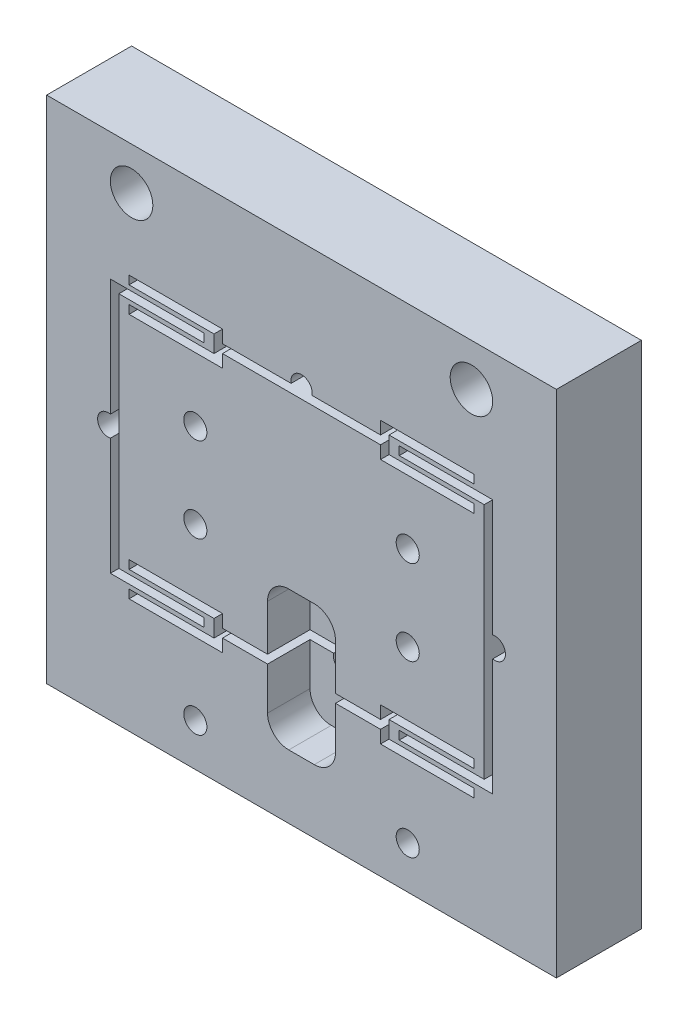
SolidWorks part; units mm, degrees
ref_plane "Front Plane" through (0, 0, 0) normal (0, 0, 1) x (1, 0, 0)
ref_plane "Top Plane" through (0, 0, 0) normal (0, 1, 0) x (1, 0, 0)
ref_plane "Right Plane" through (0, 0, 0) normal (1, 0, 0) x (0, 0, -1)
sketch "Sketch1" plane through (0, 0, 0) normal (0, 0, 1) x (1, 0, 0)
  line L1 (-38.1, 38.1) -> (38.1, 38.1)
  line L2 (-38.1, 38.1) -> (-38.1, -38.1)
  line L3 (-38.1, -38.1) -> (38.1, -38.1)
  line L4 (38.1, 38.1) -> (38.1, -38.1)
  dimension "D1" = 38.1
  dimension "D2" = 38.1
  dimension "D3" = 38.1
  dimension "D4" = 38.1
extrude "Boss-Extrude1" add sketch "Sketch1" along normal mid plane 12.7
sketch "Sketch2" plane through (0, 0, 6.35) normal (0, 0, 1) x (1, 0, 0)
  line L0 (14.605, 19.05) -> (28.575, 19.05)
  line L1 (28.575, 19.05) -> (28.575, -19.05)
  line L2 (28.575, -19.05) -> (14.605, -19.05)
  line L3 (14.605, -19.05) -> (14.605, -17.78)
  line L4 (14.605, -17.78) -> (27.305, -17.78)
  line L5 (27.305, -17.78) -> (27.305, 17.78)
  line L6 (27.305, 17.78) -> (14.605, 17.78)
  line L7 (14.605, 17.78) -> (14.605, 19.05)
  line L8 (38.1, -38.1) -> (38.1, 38.1) construction
  dimension "D1" = 38.1
  dimension "D2" = 19.05
  dimension "D3" = 9.525
  dimension "D4" = 1.27
  dimension "D5" = 12.7
  dimension "D6" = 1.27
  dimension "D7" = 1.27
extrude "Cut-Extrude1" cut sketch "Sketch2" against normal up to next (12.7 mm away)
mirror "Mirror1" about plane through (0, 0, 0) normal (1, 0, 0) of "Cut-Extrude1"
sketch "Sketch3" plane through (0, 0, 6.35) normal (0, 0, 1) x (1, 0, 0)
  line L0 (25.781, 17.145) -> (25.781, 15.875)
  line L1 (25.781, 15.875) -> (11.811, 15.875)
  line L2 (11.811, 15.875) -> (11.811, 17.78)
  line L3 (11.811, 17.78) -> (-11.811, 17.78)
  line L4 (28.575, 19.05) -> (14.605, 19.05) construction
  line L5 (14.605, 17.78) -> (27.305, 17.78) construction
  line L6 (14.605, 19.05) -> (14.605, 17.78) construction
  line L7 (27.305, 17.78) -> (27.305, -17.78) construction
  line L8 (0, 38.1) -> (0, 0) construction
  line L9 (38.1, 38.1) -> (-38.1, 38.1) construction
  line L10 (-11.811, 15.875) -> (-11.811, 17.78)
  line L11 (-25.781, 15.875) -> (-11.811, 15.875)
  line L12 (-25.781, 17.145) -> (-25.781, 15.875)
  line L13 (-11.811, 19.05) -> (11.811, 19.05)
  line L14 (11.811, 19.05) -> (11.811, 20.955)
  line L15 (11.811, 20.955) -> (25.781, 20.955)
  line L16 (25.781, 20.955) -> (25.781, 19.685)
  line L17 (25.781, 19.685) -> (13.081, 19.685)
  line L18 (13.081, 19.685) -> (13.081, 17.145)
  line L19 (13.081, 17.145) -> (25.781, 17.145)
  line L20 (-13.081, 17.145) -> (-25.781, 17.145)
  line L21 (-13.081, 19.685) -> (-13.081, 17.145)
  line L22 (-25.781, 19.685) -> (-13.081, 19.685)
  line L23 (-25.781, 20.955) -> (-25.781, 19.685)
  line L24 (-11.811, 20.955) -> (-25.781, 20.955)
  line L25 (-11.811, 19.05) -> (-11.811, 20.955)
  point P26 (0, 17.78)
  point P35 (0, 19.05)
  dimension "D1" = 0.635
  dimension "D2" = 0.635
  dimension "D3" = 1.27
  dimension "D4" = 1.27
  dimension "D5" = 1.524
  dimension "D6" = 1.524
  dimension "D7" = 1.27
extrude "Cut-Extrude2" cut sketch "Sketch3" against normal up to next (12.7 mm away)
mirror "Mirror2" about plane through (0, 0, 0) normal (0, 1, 0) of "Cut-Extrude2"
hole_wizard "1/4 (0.25) Diameter Hole1" positions "Sketch5" profile "Sketch4" hole size "1/4" standard "ANSI Inch" end condition up to next
sketch "Sketch5" plane through (0, 0, 6.35) normal (0, 0, 1) x (1, 0, 0)
  line L0 (38.1, 38.1) -> (-38.1, 38.1) construction
  point P0 (-25.4, 31.75)
  point P2 (25.4, 31.75)
  dimension "D1" = 25.4
  dimension "D2" = 25.4
  dimension "D3" = 6.35
sketch "Sketch4" plane through (-25.4, 31.75, 6.35) normal (1, 0, 0) x (0, -1, 0)
  line L0 (0, 0) -> (0, 12.7)
  line L1 (0, 12.7) -> (3.175, 12.7)
  line L2 (3.175, 12.7) -> (3.175, 0)
  line L5 (3.175, 0) -> (0, 0)
  line L11 (0, -6.35) -> (0, 107.95) construction
  dimension "Thru Hole Dia." = 6.35
  dimension "Thru Hole Depth" = 12.7
hole_wizard "#8-32 Tapped Hole1" positions "Sketch7" profile "Sketch6" tap size "#8-32" standard "ANSI Inch" end condition up to next
sketch "Sketch7" plane through (0, 0, 6.35) normal (0, 0, 1) x (1, 0, 0)
  line L0 (-38.1, -38.1) -> (38.1, -38.1) construction
  point P0 (-15.875, 6.35)
  point P2 (15.875, 6.35)
  point P4 (15.875, -6.35)
  point P6 (-15.875, -6.35)
  point P8 (-15.875, -31.75)
  point P10 (15.875, -31.75)
  dimension "D1" = 15.875
  dimension "D2" = 15.875
  dimension "D3" = 6.35
  dimension "D4" = 6.35
  dimension "D5" = 6.35
sketch "Sketch6" plane through (-15.875, 6.35, 6.35) normal (1, 0, 0) x (0, -1, 0)
  line L0 (0, 0) -> (0, 12.7)
  line L1 (0, 12.7) -> (1.7272, 12.7)
  line L2 (1.7272, 12.7) -> (1.7272, 0)
  line L5 (1.7272, 0) -> (0, 0)
  line L11 (0, -6.35) -> (0, 107.95) construction
  dimension "Thru Tap Drill Dia." = 3.4544
  dimension "Thru Tap Drill Depth" = 12.7
cosmetic thread "Hole Thread1" parameters "D2"=4.1656
cosmetic thread "Hole Thread2" parameters "D2"=4.1656
cosmetic thread "Hole Thread3" parameters "D2"=4.1656
cosmetic thread "Hole Thread4" parameters "D2"=4.1656
cosmetic thread "Hole Thread5" parameters "D2"=4.1656
cosmetic thread "Hole Thread6" parameters "D2"=4.1656
sketch "Sketch8" plane through (0, 0, 6.35) normal (0, 0, 1) x (1, 0, 0)
  line L0 (-38.1, -38.1) -> (38.1, -38.1) construction
  line L1 (-5.08, -7.747) -> (5.08, -7.747)
  line L2 (-5.08, -7.747) -> (-5.08, -28.575)
  line L3 (-5.08, -28.575) -> (5.08, -28.575)
  line L4 (5.08, -7.747) -> (5.08, -28.575)
  dimension "D1" = 5.08
  dimension "D2" = 5.08
  dimension "D3" = 20.828
  dimension "D4" = 9.525
extrude "Cut-Extrude3" cut sketch "Sketch8" against normal blind 6.35
fillet "Fillet1" radius 3.175 1 edges at (-5.08, -7.747, 3.175)
fillet "Fillet2" radius 3.175 1 edges at (-5.08, -28.575, 3.175)
fillet "Fillet3" radius 3.175 1 edges at (5.08, -7.747, 3.175)
fillet "Fillet4" radius 3.175 1 edges at (5.08, -28.575, 3.175)
sketch "Sketch11" plane through (0, 0, 6.35) normal (0, 0, 1) x (1, 0, 0)
  line L4 (27.305, 17.78) -> (27.305, -17.78) construction
  line L5 (-11.811, 17.78) -> (11.811, 17.78) construction
  line L6 (-27.305, 17.78) -> (-27.305, -17.78) construction
  line L7 (5.08, -17.78) -> (-5.08, -17.78) construction
  circle A0 centre (0, 19.3675) radius 1.5875
  circle A1 centre (28.8925, 0) radius 1.5875
  circle A2 centre (0, -19.3675) radius 1.5875
  circle A3 centre (-28.8925, 0) radius 1.5875
extrude "Cut-Extrude6" cut sketch "Sketch11" against normal up to next
